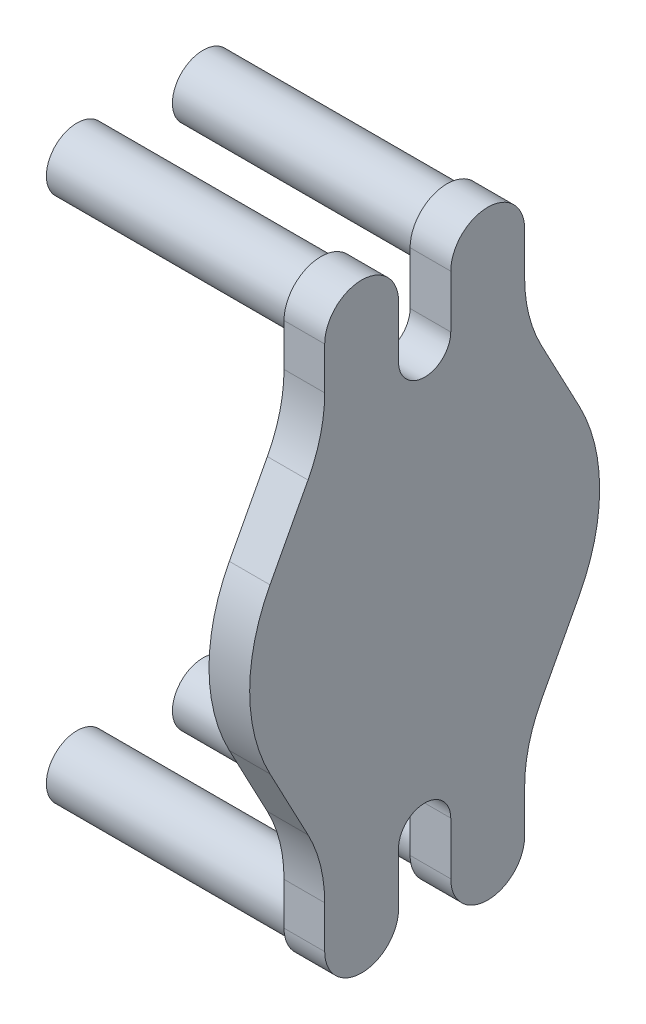
SolidWorks part; units mm, degrees
ref_plane "Front Plane" through (0, 0, 0) normal (0, 0, 1) x (1, 0, 0)
ref_plane "Top Plane" through (0, 0, 0) normal (0, 1, 0) x (1, 0, 0)
ref_plane "Right Plane" through (0, 0, 0) normal (1, 0, 0) x (0, 0, -1)
sketch "Sketch1" plane through (0, 0, 0) normal (0, 0, 1) x (1, 0, 0)
  line L0 (8.255, 0) -> (-8.255, 0) construction
  line L1 (25.4, 0) -> (-25.4, 0) construction
  line L2 (8.255, 0) -> (8.255, 18.25)
  line L3 (8.255, 18.25) -> (25.4, 18.25)
  line L4 (25.4, 18.25) -> (25.4, 0)
  line L5 (8.255, 0) -> (25.4, 0)
  point P4 (0, 0)
  point P8 (0, 0)
  dimension "D1" = 16.51
  dimension "D2" = 50.8
  dimension "D3" = 18.25
revolve "Revolve1" add sketch "Sketch1" angle 360 about L5
sketch "Sketch2" plane through (8.255, 0, 0) normal (-1, 0, 0) x (0, 0, 1)
  circle A0 centre (0, 0) radius 3.7147
  dimension "D1" = 7.4295
extrude "Cut-Extrude1" cut sketch "Sketch2" against normal blind 8.5725
sketch "Sketch3" plane through (25.4, 0, 0) normal (1, 0, 0) x (0, 0, -1)
  line L0 (-20.8953, -55) -> (-20.8953, -46.1532)
  line L1 (13.175, -55) -> (-13.175, -55) construction
  line L2 (13.175, -55) -> (13.175, 55) construction
  line L3 (13.175, 55) -> (-13.175, 55) construction
  line L4 (-13.175, -55) -> (-13.175, 55) construction
  line L5 (13.175, -55) -> (-13.175, 55) construction
  line L6 (13.175, 55) -> (-13.175, -55) construction
  line L7 (-24.3823, -32.1152) -> (-32.3245, -17.1152)
  line L9 (-5.4548, -55) -> (-5.4548, -44)
  line L11 (5.4547, -44) -> (5.4547, -55)
  line L12 (20.8953, -55) -> (20.8953, -46.1532)
  line L13 (24.3823, -32.1152) -> (32.3245, -17.1152)
  line L14 (55, 0) -> (-55, 0) construction
  line L15 (13.175, -55) -> (-13.175, 55) construction
  line L16 (13.175, 55) -> (-13.175, -55) construction
  line L17 (13.175, 55) -> (-13.175, 55) construction
  line L18 (24.3823, 32.1152) -> (32.3245, 17.1152)
  line L19 (20.8953, 55) -> (20.8953, 46.1532)
  line L20 (5.4547, 44) -> (5.4547, 55)
  line L21 (-5.4548, 55) -> (-5.4548, 44)
  line L22 (-24.3823, 32.1152) -> (-32.3245, 17.1152)
  line L23 (-20.8953, 55) -> (-20.8953, 46.1532)
  arc A15 (32.3245, -17.1152) -> (32.3245, 17.1152) centre (0, 0) ccw
  arc A16 (-5.4548, 55) -> (-20.8953, 55) centre (-13.175, 55) ccw
  arc A17 (-20.8953, -55) -> (-5.4548, -55) centre (-13.175, -55) ccw
  arc A18 (5.4547, -55) -> (20.8953, -55) centre (13.175, -55) ccw
  arc A19 (20.8953, 55) -> (5.4547, 55) centre (13.175, 55) ccw
  arc A20 (-5.4548, -44) -> (5.4547, -44) centre (0, -44) cw
  arc A21 (20.8953, -46.1532) -> (24.3823, -32.1152) centre (50.8953, -46.1532) cw
  arc A22 (-20.8953, -46.1532) -> (-24.3823, -32.1152) centre (-50.8953, -46.1532) ccw
  arc A23 (-20.8953, 46.1532) -> (-24.3823, 32.1152) centre (-50.8953, 46.1532) cw
  arc A24 (20.8953, 46.1532) -> (24.3823, 32.1152) centre (50.8953, 46.1532) ccw
  arc A25 (-5.4548, 44) -> (5.4547, 44) centre (0, 44) ccw
  arc A26 (5.4547, 55) -> (20.8953, 55) centre (13.175, 55) cw
  arc A27 (-20.8953, 55) -> (-5.4548, 55) centre (-13.175, 55) cw
  arc A29 (-32.3245, 17.1152) -> (-32.3245, -17.1152) centre (0, 0) ccw
  circle M2 centre (0, 0) radius 18.25
  dimension "D3" = 15.4405
  dimension "D5" = 7.7203
  dimension "D4" = 30
  dimension "D7" = 15
  dimension "D9" = 110
  dimension "D1" = 73.152
  dimension "D6" = 15
  dimension "D2" = 26.35
  dimension "D8" = 11
extrude "Boss-Extrude1" add sketch "Sketch3" along normal blind 8.5 separate body contours L22 A29 L7 A22 L0 A17 L9 A20 L11 A18 L12 A21 L13 A15 L18 A24 L19 A19 L20 A25 L21 A16 L23 A23 M2 | M2
sketch "Sketch4" plane through (25.4, 0, 0) normal (-1, 0, 0) x (0, 0, 1)
  line L0 (-20.8953, 55) -> (-5.4547, 55) construction
  line L1 (13.175, -55) -> (-13.175, -55) construction
  line L2 (13.175, -55) -> (13.175, 55) construction
  line L3 (13.175, 55) -> (-13.175, 55) construction
  line L4 (-13.175, -55) -> (-13.175, 55) construction
  line L5 (13.175, -55) -> (-13.175, 55) construction
  line L6 (13.175, 55) -> (-13.175, -55) construction
  circle A0 centre (-13.175, 55) radius 4.75
  circle A1 centre (13.175, -55) radius 4.75
  circle A2 centre (13.175, 55) radius 4.75
  circle A3 centre (-13.175, -55) radius 4.75
  arc A4 (-5.4547, 55) -> (-20.8953, 55) centre (-13.175, 55) ccw construction
  circle A5 centre (-13.175, 55) radius 6.4
  circle A6 centre (13.175, 55) radius 6.4
  circle A7 centre (13.175, -55) radius 6.4
  circle A8 centre (-13.175, -55) radius 6.4
  point P6 (0, 0)
  dimension "D1" = 9.5
  dimension "D2" = 12.8
extrude "Boss-Extrude2" add sketch "Sketch4" along normal blind 51
sketch "Sketch5" plane through (8.255, 0, 0) normal (-1, 0, 0) x (0, 0, 1)
  circle A0 centre (0, 0) radius 18.25
  dimension "D1" = 36.5
extrude "Cut-Extrude2" cut sketch "Sketch5" against normal blind 22.15
